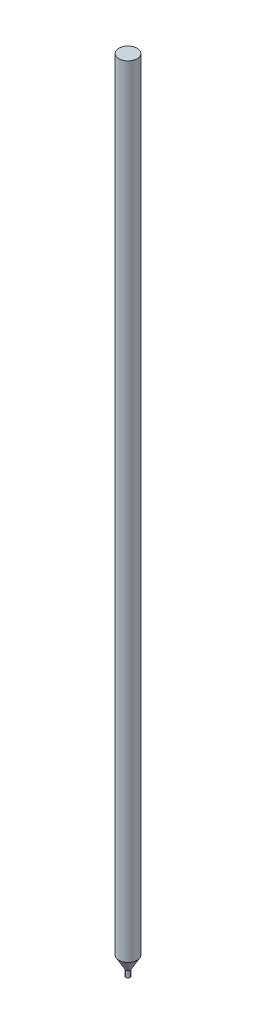
SolidWorks part; units mm, degrees
material "ABS"
ref_plane "Front Plane" through (0, 0, 0) normal (0, 0, 1) x (1, 0, 0)
ref_plane "Top Plane" through (0, 0, 0) normal (0, 1, 0) x (1, 0, 0)
ref_plane "Right Plane" through (0, 0, 0) normal (1, 0, 0) x (0, 0, -1)
sketch "Sketch1" plane through (0, 0, 0) normal (0, 1, 0) x (1, 0, 0)
  circle A0 centre (0, 0) radius 0.875
  dimension "D1" = 1.75
extrude "Boss-Extrude1" add sketch "Sketch1" along normal blind 75
sketch "Sketch2" plane through (0, 0, 0) normal (1, 0, 0) x (0, 0, -1)
  line L0 (0, 0) -> (0, -1.7691)
  line L1 (-0.875, 0) -> (0.875, 0) construction
  line L2 (0, -1.7691) -> (0.2, -1.7691)
  line L3 (0.2, -1.7691) -> (0.2, -1.1691)
  line L4 (0.2, -1.1691) -> (0.875, 0)
  line L5 (0.875, 0) -> (0, 0)
  dimension "D1" = 60
  dimension "D2" = 0.6
  dimension "D3" = 0.2
revolve "Revolve1" add sketch "Sketch2" angle 360 about L0
